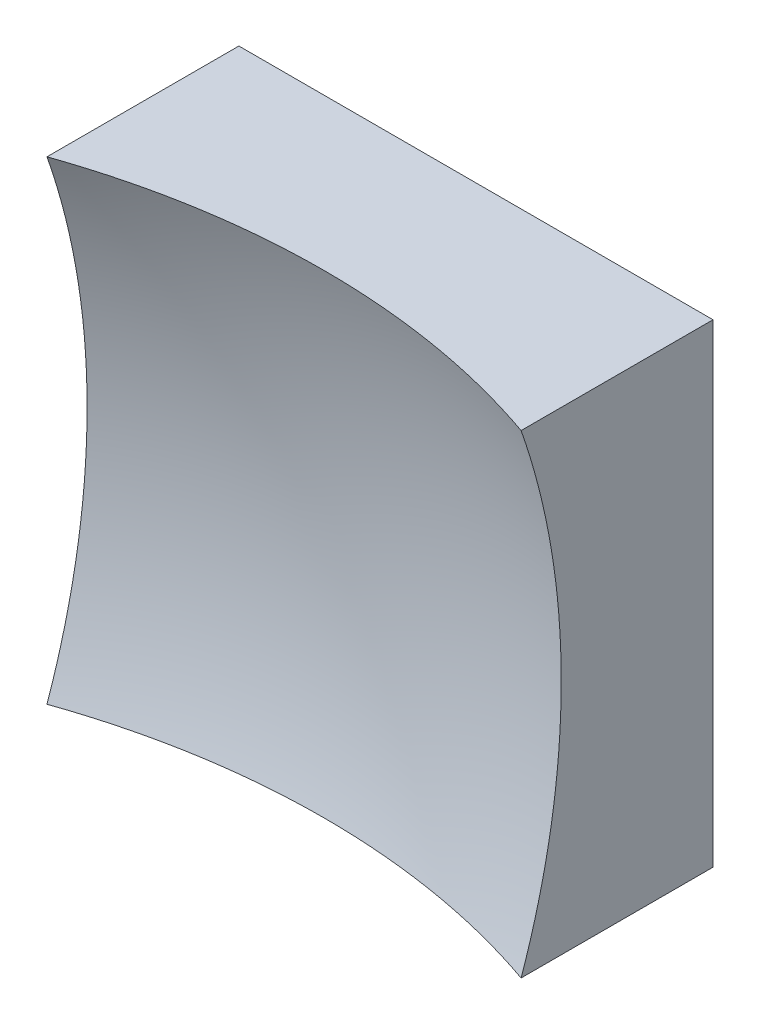
SolidWorks part; units mm, degrees
ref_plane "前视基准面" through (0, 0, 0) normal (0, 0, 1) x (1, 0, 0)
ref_plane "上视基准面" through (0, 0, 0) normal (0, 1, 0) x (1, 0, 0)
ref_plane "右视基准面" through (0, 0, 0) normal (1, 0, 0) x (0, 0, -1)
sketch "草图1" plane through (0, 0, 0) normal (0, 0, 1) x (1, 0, 0)
  line L1 (-12.5, 12.5) -> (12.5, 12.5)
  line L2 (-12.5, 12.5) -> (-12.5, -12.5)
  line L3 (-12.5, -12.5) -> (12.5, -12.5)
  line L4 (12.5, 12.5) -> (12.5, -12.5)
  line L5 (-12.5, 12.5) -> (12.5, -12.5) construction
  line L6 (-12.5, -12.5) -> (12.5, 12.5) construction
  point P0 (0, 0)
  dimension "D1" = 25
  dimension "D2" = 25
extrude "凸台-拉伸1" add sketch "草图1" along normal blind 20 contours L2 L3 L4 L1
sketch "草图2" plane through (0, 0, 0) normal (0, 1, 0) x (1, 0, 0)
  line L0 (-7.4603, -6) -> (7.3192, -6) construction
  line L1 (0, 0) -> (0, -12.1749) construction
  line L2 (38.9938, -37.0847) -> (0, -37.0847)
  line L3 (0, -37.0847) -> (0, -6)
  arc A1 (38.9938, -37.0847) -> (0, -6) centre (0, -46) ccw
  dimension "D2" = 80
  dimension "D1" = 6
revolve "切除-旋转2" cut sketch "草图2" angle 360 about L3
